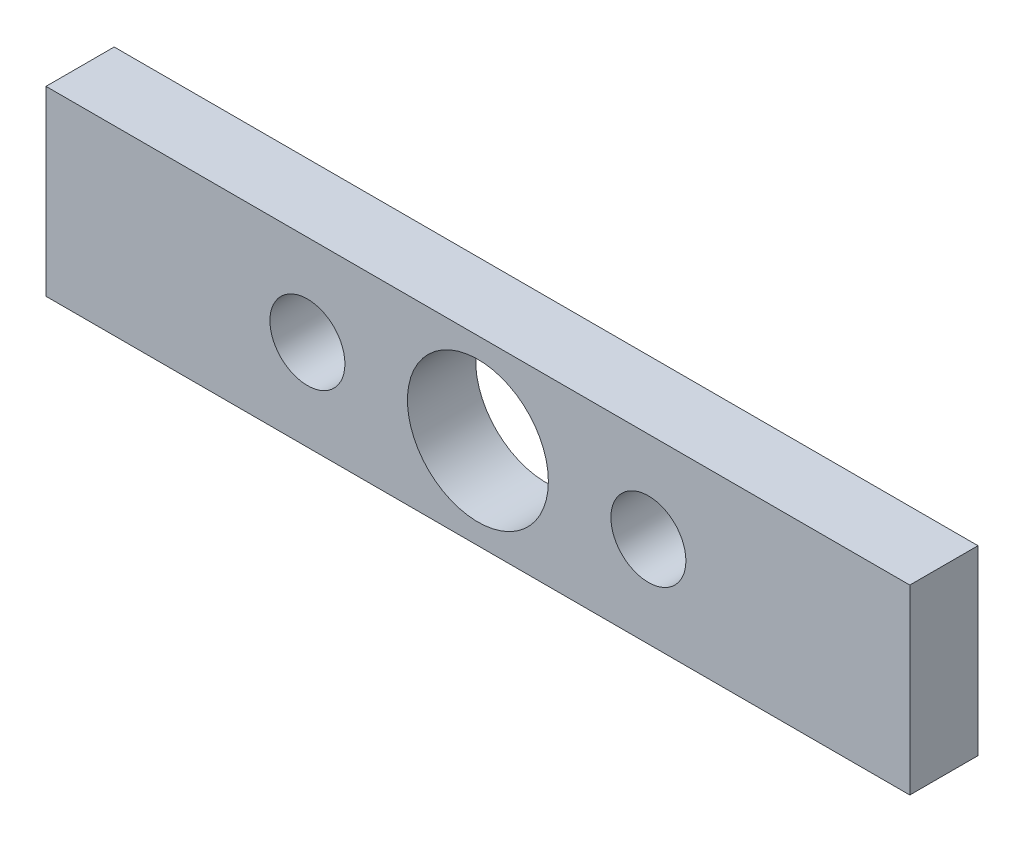
SolidWorks part; units mm, degrees
material "PTFE (general)"
ref_plane "Front Plane" through (0, 0, 0) normal (0, 0, 1) x (1, 0, 0)
ref_plane "Top Plane" through (0, 0, 0) normal (0, 1, 0) x (1, 0, 0)
ref_plane "Right Plane" through (0, 0, 0) normal (1, 0, 0) x (0, 0, -1)
sketch "Sketch1" plane through (0, 0, 0) normal (0, 0, 1) x (1, 0, 0)
  line L1 (-19, 0) -> (19, 0)
  line L2 (-19, 0) -> (-19, 8)
  line L3 (-19, 8) -> (19, 8)
  line L4 (19, 0) -> (19, 8)
  dimension "D1" = 8
  dimension "D2" = 38
extrude "Boss-Extrude1" add sketch "Sketch1" along normal blind 3
sketch "Sketch2" plane through (0, 0, 3) normal (0, 0, 1) x (1, 0, 0)
  line L0 (0, 0) -> (0, 8) construction
  line L1 (-19, 0) -> (19, 0) construction
  line L2 (19, 8) -> (-19, 8) construction
  line L3 (-19, 8) -> (-19, 0) construction
  line L4 (-19, 4) -> (19, 4) construction
  line L5 (19, 0) -> (19, 8) construction
  circle A0 centre (0, 4) radius 3.1
  circle A1 centre (-7.5, 4) radius 1.65
  circle A2 centre (7.5, 4) radius 1.65
  dimension "D1" = 6.2
  dimension "D2" = 3.3
  dimension "D3" = 7.5
  dimension "D4" = 15
extrude "Cut-Extrude1" cut sketch "Sketch2" against normal through all
